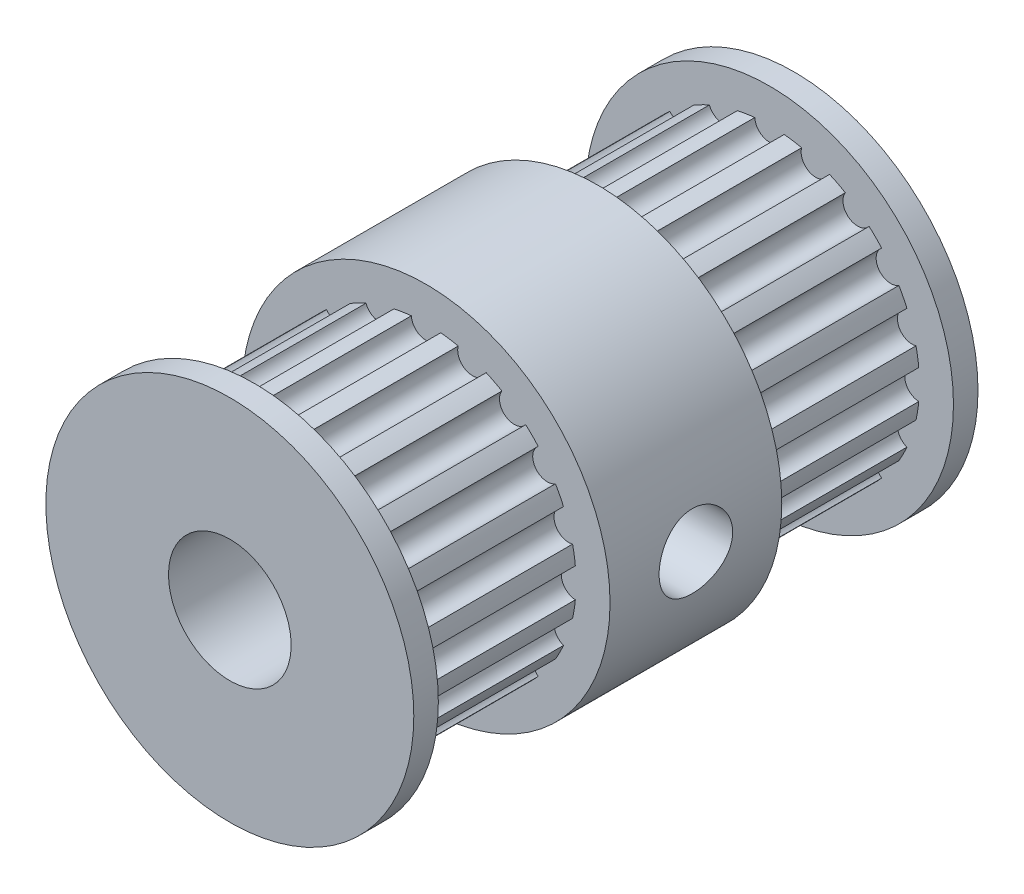
SolidWorks part; units mm, degrees
material "6061 合金"
ref_plane "前基準面" through (0, 0, 0) normal (0, 0, 1) x (1, 0, 0)
ref_plane "上基準面" through (0, 0, 0) normal (0, 1, 0) x (1, 0, 0)
ref_plane "右基準面" through (0, 0, 0) normal (1, 0, 0) x (0, 0, -1)
sketch "草圖1" plane through (0, 0, 0) normal (0, 0, 1) x (1, 0, 0)
  circle A0 centre (0, 0) radius 7.5
  dimension "D1" = 15
extrude "填料-伸長1" add sketch "草圖1" along normal mid plane 7
sketch "草圖2" plane through (0, 0, 3.5) normal (0, 0, 1) x (1, 0, 0)
  circle A0 centre (0, 0) radius 6.115
  dimension "D1" = 12.23
extrude "填料-伸長2" add sketch "草圖2" along normal blind 7
sketch "草圖7" plane through (0, 0, 10.5) normal (0, 0, 1) x (1, 0, 0)
  line L0 (0, 0) -> (0, 6.115) construction
  arc A0 (-0.5993, 6.0856) -> (0.5993, 6.0856) centre (0, 6.115) ccw
  circle A1 centre (0, 0) radius 6.115 construction
  circle A2 centre (0, 0) radius 6.115 construction
  arc A3 (-0.5993, 6.0856) -> (0.5993, 6.0856) centre (0, 0) cw
  point P10 (0, 5.515)
  dimension "D1" = 0.6
extrude "除料-伸長3" cut sketch "草圖7" against normal up to surface (14 mm away)
sketch "草圖3" plane through (0, 0, 10.5) normal (0, 0, 1) x (1, 0, 0)
  circle A0 centre (0, 0) radius 7.5
  circle A1 centre (0, 0) radius 7.5 construction
extrude "填料-伸長3" add sketch "草圖3" along normal blind 1
sketch "草圖5" plane through (0, 0, 0) normal (0, 1, 0) x (1, 0, 0)
  circle A0 centre (0, 0) radius 1.5
  dimension "D1" = 3
extrude "除料-伸長1" cut sketch "草圖5" against normal up to next (7.5 mm away)
pattern_circular "環狀複製排列1" count 2 every 90 about axis through (0, 0, 3.5) along (0, 0, -1) of "除料-伸長1"
pattern_circular "環狀複製排列2" count 20 over 360 about axis through (0, 0, 0) along (0, 0, 1) of "除料-伸長3"
mirror "鏡射7" about plane through (0, 0, 0) normal (0, 0, 1) of "環狀複製排列2", "填料-伸長2", "填料-伸長3", "除料-伸長3"
sketch "草圖6" plane through (0, 0, -3.5) normal (0, 0, -1) x (-1, 0, 0)
  circle A0 centre (0, 0) radius 2.5
  dimension "D1" = 5
extrude "除料-伸長2" cut sketch "草圖6" against normal through all both and the other way through all
